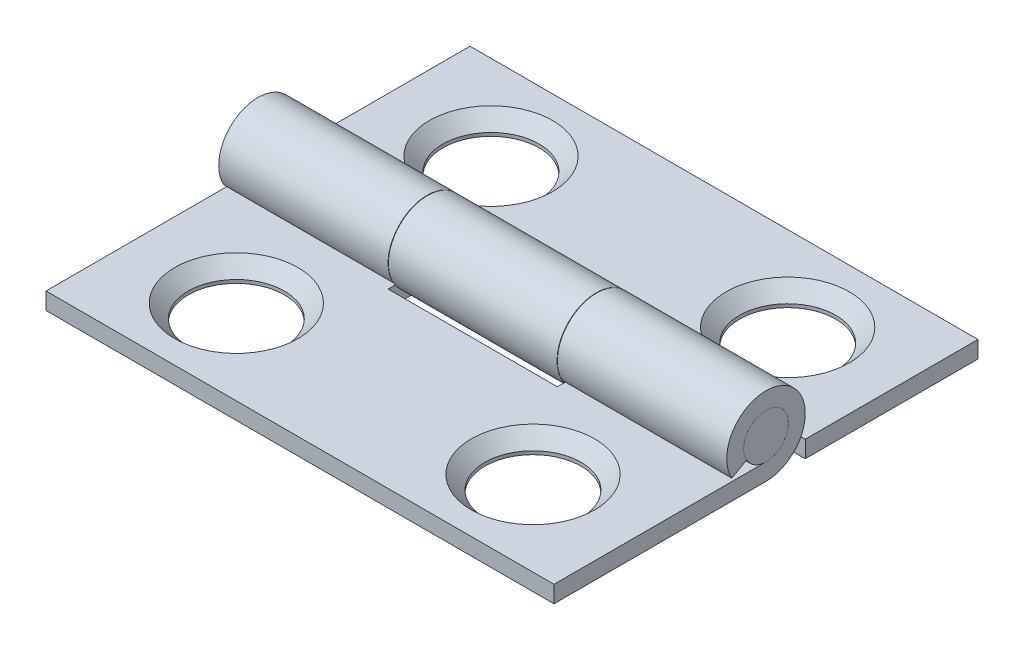
SolidWorks part; units mm, degrees
ref_plane "Front Plane" through (0, 0, 0) normal (0, 0, 1) x (1, 0, 0)
ref_plane "Top Plane" through (0, 0, 0) normal (0, 1, 0) x (1, 0, 0)
ref_plane "Right Plane" through (0, 0, 0) normal (1, 0, 0) x (0, 0, -1)
sketch "Sketch1" plane through (0, 0, 0) normal (0, 1, 0) x (1, 0, 0)
  line L0 (-9.525, 0) -> (9.525, 0) construction
  line L1 (-9.525, -7.9502) -> (-9.525, 7.9502) construction
  line L2 (-9.525, -7.9502) -> (-5.5626, -7.9502) construction
  line L3 (5.5626, -4.7752) -> (-5.5626, -4.7752) construction
  line L4 (-5.5626, -7.9502) -> (5.5626, -7.9502) construction
  line L5 (9.525, -7.9502) -> (9.525, -4.7752) construction
  line L6 (5.5626, -7.9502) -> (9.525, -7.9502) construction
  line L7 (-9.525, 7.9502) -> (-4.7498, 7.9502) construction
  line L8 (-4.7498, 7.9502) -> (11.1252, 7.9502) construction
  line L9 (11.1252, 7.9502) -> (27.0002, 7.9502) construction
  line L10 (27.0002, 7.9502) -> (30.9626, 7.9502) construction
  line L11 (5.5626, -7.0866) -> (5.5626, -2.4638) construction
  line L12 (5.5626, -4.7752) -> (9.525, -4.7752) construction
  line L13 (-5.5626, -4.7752) -> (-5.5626, -7.9502) construction
  line L14 (5.5626, 4.7752) -> (-5.5626, 4.7752) construction
  point P3 (5.5626, -6.5786)
  point P4 (0, 0)
  point P8 (-9.525, 0)
  point P17 (-3.175, 0)
  point P21 (5.5626, -4.7752)
  dimension "Frame Leaf Height" = 19.05
  dimension "Overall Width" = 15.9004
  dimension "Hole to End 1" = 3.9624
  dimension "Hole to End 2" = 3.9624
  dimension "D1" = 3.9624
  dimension "D2" = 4.7752
  dimension "D4" = 15.875
  dimension "D6" = 15.875
  dimension "Knuckle Length" = 6.35
  dimension "Hole Chamfer Dia" = 4.6228
  dimension "Hole Center to Pin" = 4.7752
  dimension "Door Leaf Height" = 19.05
  dimension "Mounting Hole Diameter" = 3.6068
  dimension "D3" = 11.1252
  dimension "Frame Leaf Width" = 7.9502
  dimension "Door Leaf Width" = 7.9502
sketch "Sketch2" plane through (0, 0, 0) normal (1, 0, 0) x (0, 0, -1)
  line L2 (0, -1.4732) -> (0, -0.8382) construction
  line L4 (0, 0.8382) -> (0, -0.8382) construction
  point P8 (0, 0)
  dimension "Leaf Thickness" = 0.635
  dimension "Pin Diameter" = 1.6764
sketch "Sketch3" plane through (0, 0, 0) normal (1, 0, 0) x (0, 0, -1)
  line L3 (0, 0) -> (-1.4732, -0.8382) construction
  line L4 (0, -1.4732) -> (-7.9502, -1.4732)
  line L5 (-7.9502, -1.4732) -> (-7.9502, -0.8382)
  line L7 (-7.9502, -0.8382) -> (0, -0.8382)
  line L8 (-7.9502, 0) -> (7.9502, 0) construction
  line L9 (-0.7285, -0.4145) -> (-1.2805, -0.7285)
  line L11 (-1.4732, 0) -> (-1.4732, -0.8382) construction
  circle A4 centre (0, 0) radius 0.8382 construction
  circle A5 centre (0, 0) radius 1.4732 construction
  arc A8 (-0.7285, -0.4145) -> (0, -0.8382) centre (0, 0) cw
  arc A9 (-1.2805, -0.7285) -> (0, -1.4732) centre (0, 0) cw
  point P0 (-1.2805, -0.7285)
  point P13 (-0.7285, -0.4145)
extrude "Boss-Extrude1" add sketch "Sketch3" along normal mid plane 19.05
pattern_circular "CirPattern1" count 2 over 360 about axis through (0, 0, 0) along (0, 1, 0) of bodies 104 107
sketch "Sketch4" plane through (0, 0, 0) normal (0, 1, 0) x (1, 0, 0)
  line L0 (-9.525, -1.4732) -> (9.525, -1.4732) construction
  line L1 (-9.525, -1.4732) -> (9.525, -1.4732) construction
  line L2 (9.525, 1.4732) -> (-9.525, 1.4732) construction
  line L3 (9.525, 1.4732) -> (-9.525, 1.4732) construction
  line L4 (-3.175, -1.4732) -> (-3.175, 1.4732)
  line L6 (-3.175, 1.4732) -> (3.175, 1.4732)
  line L7 (3.175, -1.4732) -> (-3.175, -1.4732)
  line L8 (3.175, 1.4732) -> (3.175, -1.4732)
  point P8 (-3.175, 0)
  dimension "D1" = 6.35
extrude "Cut-Extrude1" cut sketch "Sketch4" against normal through all both and the other way through all
sketch "Sketch10" plane through (0, 0, 0) normal (0, 1, 0) x (1, 0, 0)
  line L0 (9.525, 1.4732) -> (-9.525, 1.4732) construction
  line L5 (-3.1623, 1.4732) -> (-9.525, 1.4732)
  line L6 (-3.1623, 1.4732) -> (-3.1623, -1.4732)
  line L7 (-3.1623, -1.4732) -> (-9.525, -1.4732)
  line L8 (-9.525, 1.4732) -> (-9.525, -1.4732)
  line L9 (3.1623, 1.4732) -> (9.525, 1.4732)
  line L10 (3.1623, 1.4732) -> (3.1623, -1.4732)
  line L11 (3.1623, -1.4732) -> (9.525, -1.4732)
  line L12 (9.525, 1.4732) -> (9.525, -1.4732)
  dimension "D1" = 0.0127
extrude "Cut-Extrude4" cut sketch "Sketch10" against normal through all both and the other way through all
sketch "Sketch5" plane through (0, -0.8382, 0) normal (0, 1, 0) x (1, 0, 0)
  line L0 (5.5626, -4.7752) -> (-5.5626, -4.7752) construction
  line L1 (0, -4.7752) -> (0, -7.9502) construction
  line L2 (-5.5626, -4.7752) -> (-5.5626, -7.9502) construction
  line L3 (9.525, -7.9502) -> (-9.525, -7.9502) construction
  circle A0 centre (5.5626, -4.7752) radius 2.3114
  circle A2 centre (-5.5626, -4.7752) radius 2.3114
extrude "Cut-Extrude2" cut sketch "Sketch5" against normal through all draft 45
sketch "Sketch9" plane through (0, 0, 0) normal (0, 1, 0) x (1, 0, 0)
  circle A0 centre (5.5626, -4.7752) radius 1.8034
  circle A2 centre (-5.5626, -4.7752) radius 1.8034
  dimension "D1" = 3.6068
extrude "Cut-Extrude3" cut sketch "Sketch9" against normal through all both and the other way through all
sketch "Sketch11" plane through (0, -0.8382, 0) normal (0, 1, 0) x (1, 0, 0)
  circle A0 centre (5.5626, 4.7752) radius 2.3114
  circle A1 centre (-5.5626, 4.7752) radius 2.3114
  circle A2 centre (-5.5626, -4.7752) radius 2.3114 construction
extrude "Cut-Extrude5" cut sketch "Sketch11" against normal through all draft 45
sketch "Sketch12" plane through (0, -0.8382, 0) normal (0, 1, 0) x (1, 0, 0)
  circle A0 centre (-5.5626, 4.7752) radius 1.8034
  circle A1 centre (5.5626, 4.7752) radius 1.8034
  circle A2 centre (-5.5626, -4.7752) radius 1.8034 construction
extrude "Cut-Extrude6" cut sketch "Sketch12" against normal through all both and the other way through all
sketch "Sketch6" plane through (0, 0, 0) normal (1, 0, 0) x (0, 0, -1)
  circle A0 centre (0, 0) radius 0.8382
  dimension "D1" = 1.6764
extrude "Boss-Extrude2" add sketch "Sketch6" along normal mid plane 19.05 separate body
sketch "Sketch7" plane through (0, 0, 0) normal (1, 0, 0) x (0, 0, -1)
  line L0 (-0.8382, 0) -> (0.8382, 0) construction
  line L1 (-7.9502, 0) -> (7.9502, 0) construction
  line L2 (7.9502, -0.8382) -> (7.9502, -1.4732) construction
  line L3 (7.9502, -0.8382) -> (7.9502, -1.4732) construction
  line L4 (7.9502, -1.4732) -> (-7.9502, -1.4732) construction
  line L5 (-7.9502, -1.4732) -> (-7.9502, -0.8382)
  point P6 (0, 0)
  point P8 (0.8382, 0)
  point P9 (-0.8382, 0)
  point P12 (7.9502, -0.8382)
  point P13 (7.9502, -1.4732)
  point P14 (-7.9502, -1.4732)
  dimension "D1" = 1.6764
  dimension "D2" = 15.9004
  dimension "D3" = 0.635
sketch "Sketch8" plane through (0, 0, 0) normal (0, 1, 0) x (1, 0, 0)
  line L0 (-7.874, -4.7752) -> (-3.2512, -4.7752) construction
  line L1 (5.5626, 4.7752) -> (-5.5626, 4.7752) construction
  line L2 (3.2512, -4.7752) -> (7.874, -4.7752) construction
  line L3 (-5.5626, -2.4638) -> (-5.5626, -7.0866) construction
  line L5 (5.5626, -2.4638) -> (5.5626, -7.0866) construction
  line L6 (-5.5626, 7.0866) -> (-5.5626, 2.4638) construction
  line L7 (-7.874, 4.7752) -> (-3.2512, 4.7752) construction
  line L10 (5.5626, 7.0866) -> (5.5626, 2.4638) construction
  line L11 (3.2512, 4.7752) -> (7.874, 4.7752) construction
  line L12 (5.5626, 4.7752) -> (7.197, 6.4096) construction
  circle A1 centre (-5.5626, -4.7752) radius 2.3114 construction
  circle A3 centre (5.5626, -4.7752) radius 2.3114 construction
  circle A7 centre (5.5626, 4.7752) radius 2.3114 construction
  circle A8 centre (-5.5626, 4.7752) radius 2.3114 construction
  circle A9 centre (5.5626, 4.7752) radius 2.3114 construction
  point P2 (-9.525, 0)
  point P7 (-5.5626, -4.7752)
  point P19 (5.5626, -4.7752)
  point P25 (-9.525, 7.9502)
  point P26 (30.9626, 7.9502)
  point P28 (-9.525, -7.9502)
  point P30 (9.525, -7.9502)
  point P32 (-7.874, -4.7752)
  point P33 (-5.5626, -2.4638)
  point P34 (-3.2512, -4.7752)
  point P35 (-5.5626, -7.0866)
  point P40 (7.874, -4.7752)
  point P41 (5.5626, -7.0866)
  point P42 (3.2512, -4.7752)
  point P43 (5.5626, -2.4638)
  point P67 (5.5626, -7.9502)
  point P69 (-5.5626, -7.9502)
  point P71 (-4.7498, 7.9502)
  point P73 (-5.5626, 4.7752)
  point P76 (5.5626, 4.7752)
  point P77 (27.0002, 7.9502)
  point P78 (11.1252, 7.9502)
  point P82 (-5.5626, 7.0866)
  point P83 (-7.874, 4.7752)
  point P84 (-5.5626, 2.4638)
  point P85 (-3.2512, 4.7752)
  point P90 (5.5626, 2.4638)
  point P91 (3.2512, 4.7752)
  point P92 (5.5626, 7.0866)
  point P97 (7.197, 6.4096)
  dimension "D1" = 45
equation "\"D1@Sketch1\"=\"Hole to End 1@Sketch1\""
equation "\"D6@Sketch1\"=\"D4@Sketch1\""
equation "\"D1@Boss-Extrude1\" = \"Frame Leaf Height@Sketch1\""
equation "\"D1@Sketch4\"=\"Knuckle Length@Sketch1\""
equation "\"D1@Sketch6\"=\"Pin Diameter@Sketch2\""
equation "\"D1@Boss-Extrude2\" = \"Frame Leaf Height@Sketch1\""
equation "\"D1@Sketch7\"=\"Pin Diameter@Sketch2\""
equation "\"D2@Sketch7\"=\"Overall Width@Sketch1\""
equation "\"D3@Sketch7\"=\"Leaf Thickness@Sketch2\""
equation "\"Knuckle Length@Sketch1\"=\"Frame Leaf Height@Sketch1\" / 3"
equation "\"Hole to End 2@Sketch1\"=\"Hole to End 1@Sketch1\""
equation "\"D1@Sketch9\"=\"Mounting Hole Diameter@Sketch1\""
equation "\"Hole Chamfer Dia@Sketch1\"=\"Mounting Hole Diameter@Sketch1\"+.04"
